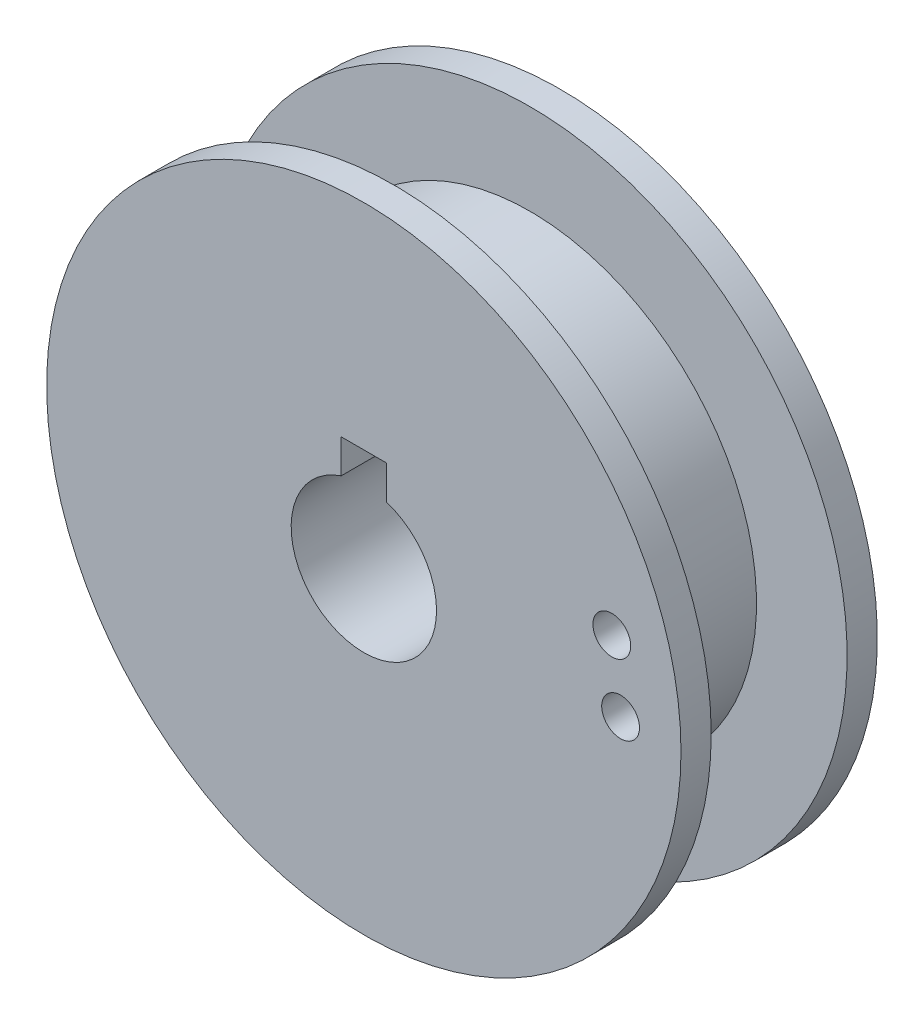
SolidWorks part; units mm, degrees
ref_plane "Piano frontale" through (0, 0, 0) normal (0, 0, 1) x (1, 0, 0)
ref_plane "Piano superiore" through (0, 0, 0) normal (0, 1, 0) x (1, 0, 0)
ref_plane "Piano destro" through (0, 0, 0) normal (1, 0, 0) x (0, 0, -1)
sketch "Sketch1" plane through (0, 0, 0) normal (0, 0, 1) x (1, 0, 0)
  circle A0 centre (0, 0) radius 21
  dimension "D1" = 42
extrude "Side 1" add sketch "Sketch1" along normal blind 2
sketch "Sketch2" plane through (0, 0, 0) normal (0, 0, -1) x (-1, 0, 0)
  circle A0 centre (0, 0) radius 15
  dimension "D1" = 30
extrude "Pulley" add sketch "Sketch2" along normal blind 9
sketch "Sketch3" plane through (0, 0, -9) normal (0, 0, -1) x (-1, 0, 0)
  circle A0 centre (0, 0) radius 21
  dimension "D1" = 42
extrude "Side 2" add sketch "Sketch3" along normal blind 2
sketch "Sketch4" plane through (0, 0, -11) normal (0, 0, -1) x (-1, 0, 0)
  circle A0 centre (0, 0) radius 4.8125
  dimension "D1" = 9.625
extrude "ShaftHole" cut sketch "Sketch4" against normal blind 13
sketch "Sketch5" plane through (0, 0, -11) normal (0, 0, -1) x (-1, 0, 0)
  line L0 (0, 0) -> (0, 4.8125) construction
  line L2 (-1.5, 2.8125) -> (1.5, 2.8125)
  line L3 (-1.5, 2.8125) -> (-1.5, 6.8125)
  line L4 (-1.5, 6.8125) -> (1.5, 6.8125)
  line L5 (1.5, 2.8125) -> (1.5, 6.8125)
  line L6 (-1.5, 2.8125) -> (1.5, 6.8125) construction
  line L7 (-1.5, 6.8125) -> (1.5, 2.8125) construction
  circle A0 centre (0, 0) radius 4.8125 construction
  circle A1 centre (0, 0) radius 4.8125 construction
  dimension "D1" = 3
  dimension "D2" = 4
extrude "KeyWay" cut sketch "Sketch5" against normal blind 13
sketch "Sketch6" plane through (0, 0, 2) normal (0, 0, 1) x (1, 0, 0)
  line L0 (0, 0) -> (21, 0) construction
  line L1 (0, 0) -> (20.2844, 5.4352) construction
  line L2 (16.4207, 4.3999) -> (16.4207, 0) construction
  circle A0 centre (17, 0) radius 1.25
  circle A1 centre (0, 0) radius 21 construction
  circle A2 centre (16.4207, 4.3999) radius 1.25
  circle A3 centre (0, 0) radius 17 construction
  dimension "D2" = 2.5
  dimension "D3" = 2.5
  dimension "D1" = 34
  dimension "D5" = 15
  dimension "D6" = 4.3999
  dimension "D7" = 0.5793
extrude "CableHole" cut sketch "Sketch6" against normal blind 2
